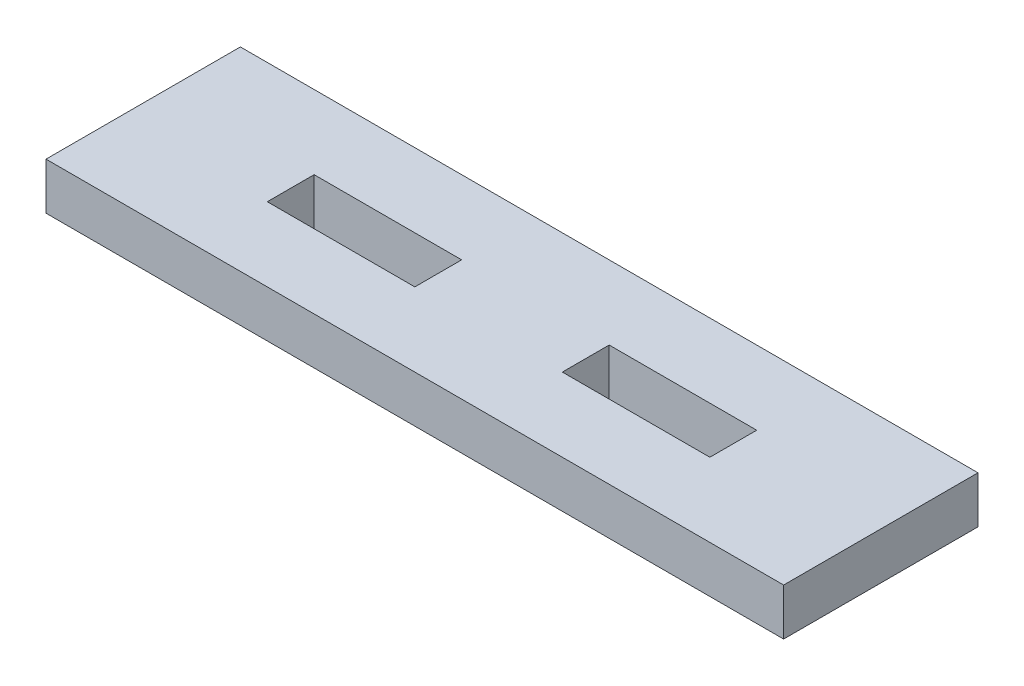
SolidWorks part; units mm, degrees
ref_plane "Front Plane" through (0, 0, 0) normal (0, 0, 1) x (1, 0, 0)
ref_plane "Top Plane" through (0, 0, 0) normal (0, 1, 0) x (1, 0, 0)
ref_plane "Right Plane" through (0, 0, 0) normal (1, 0, 0) x (0, 0, -1)
sketch "Sketch1" plane through (0, 0, 0) normal (0, 1, 0) x (1, 0, 0)
  line L0 (0, 6.5875) -> (8.175, 6.5875) construction
  line L1 (0, 0) -> (50, 0)
  line L2 (0, 0) -> (0, 13.175)
  line L3 (0, 13.175) -> (50, 13.175)
  line L4 (50, 0) -> (50, 13.175)
  line L5 (25, 13.175) -> (25, 0) construction
  line L6 (0, 6.5875) -> (50, 6.5875) construction
  line L7 (8.175, 6.5875) -> (15, 6.5875) construction
  line L8 (30, 5) -> (40, 5)
  line L9 (10, 5) -> (20, 5)
  line L10 (10, 5) -> (10, 8.175)
  line L11 (10, 8.175) -> (20, 8.175)
  line L12 (20, 5) -> (20, 8.175)
  line L13 (10, 5) -> (20, 8.175) construction
  line L14 (10, 8.175) -> (20, 5) construction
  line L15 (30, 5) -> (30, 8.175)
  line L16 (30, 8.175) -> (40, 8.175)
  line L17 (40, 5) -> (40, 8.175)
  line L18 (28.175, 6.5875) -> (35, 6.5875) construction
  line L19 (30, 5) -> (40, 8.175) construction
  line L20 (30, 8.175) -> (40, 5) construction
  point P12 (0, 0)
  point P19 (0, 0)
  point P28 (25, 6.5875)
  dimension "D1" = 2
  dimension "D2" = 13.175
  dimension "D3" = 50
  dimension "D4" = 10
  dimension "D5" = 10
  dimension "D6" = 3.175
  dimension "D7" = 10
extrude "Boss-Extrude1" add sketch "Sketch1" along normal blind 3.175
